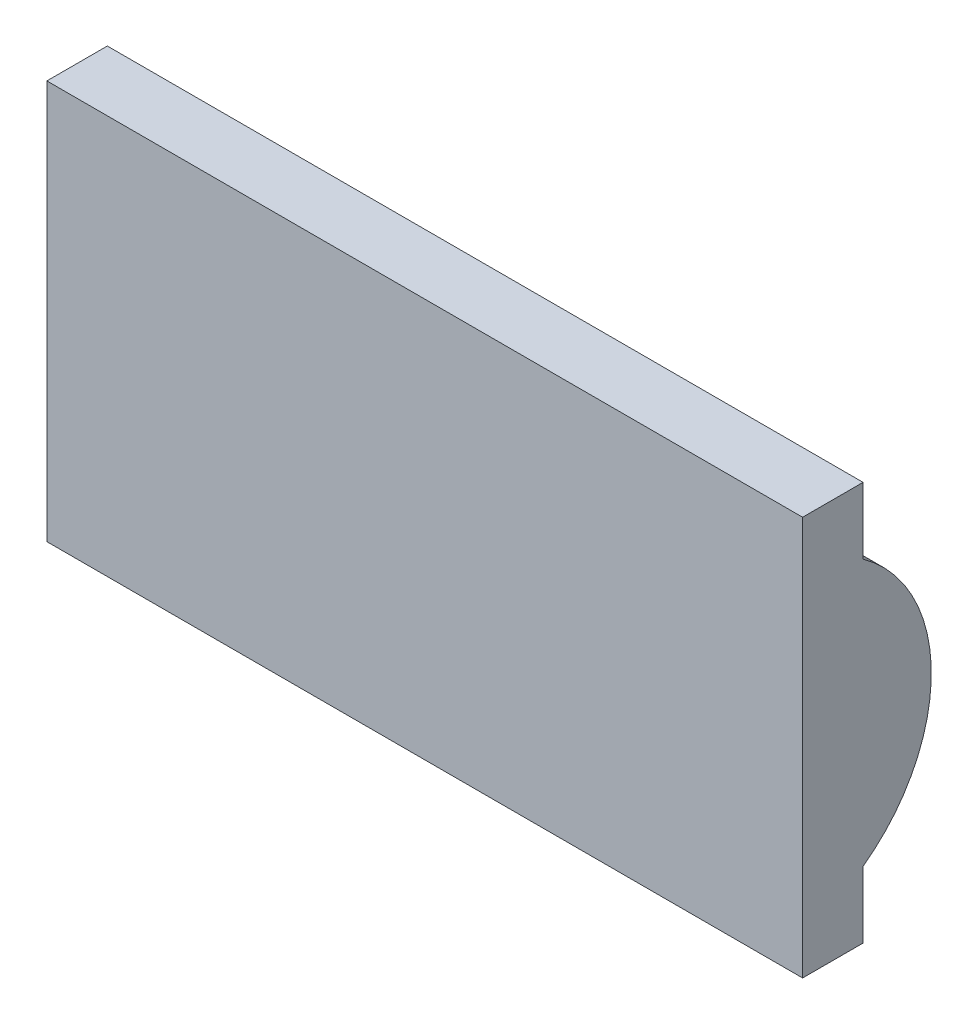
SolidWorks part; units mm, degrees
ref_plane "Front Plane" through (0, 0, 0) normal (0, 0, 1) x (1, 0, 0)
ref_plane "Top Plane" through (0, 0, 0) normal (0, 1, 0) x (1, 0, 0)
ref_plane "Right Plane" through (0, 0, 0) normal (1, 0, 0) x (0, 0, -1)
sketch "Sketch2" plane through (0, 0, 0) normal (1, 0, 0) x (0, 0, -1)
  line L0 (0, 25.6884) -> (0, -7.3116)
  line L1 (0, -7.3116) -> (5, -7.3116)
  line L2 (0, 25.6884) -> (5, 25.6884)
  line L3 (5, 25.6884) -> (5, 20.1884)
  line L4 (5, -7.3116) -> (5, -1.8116)
  line L5 (-26.1288, 9.1884) -> (40.129, 9.1884) construction
  arc A0 (5, 20.1884) -> (5, -1.8116) centre (-2.9009, 9.1884) cw
  dimension "D6" = 16.5
  dimension "D1" = 5
  dimension "D2" = 5
  dimension "D3" = 33
  dimension "D4" = 5.5
  dimension "D5" = 5.5
  dimension "D7" = 66.2578
extrude "Boss-Extrude1" add sketch "Sketch2" along normal blind 62.5
sketch "Sketch3" plane through (0, 25.6884, 0) normal (0, 1, 0) x (1, 0, 0)
  line L0 (62.5, 5) -> (0, 5)
  circle A0 centre (31.25, -26.25) radius 44.1942
